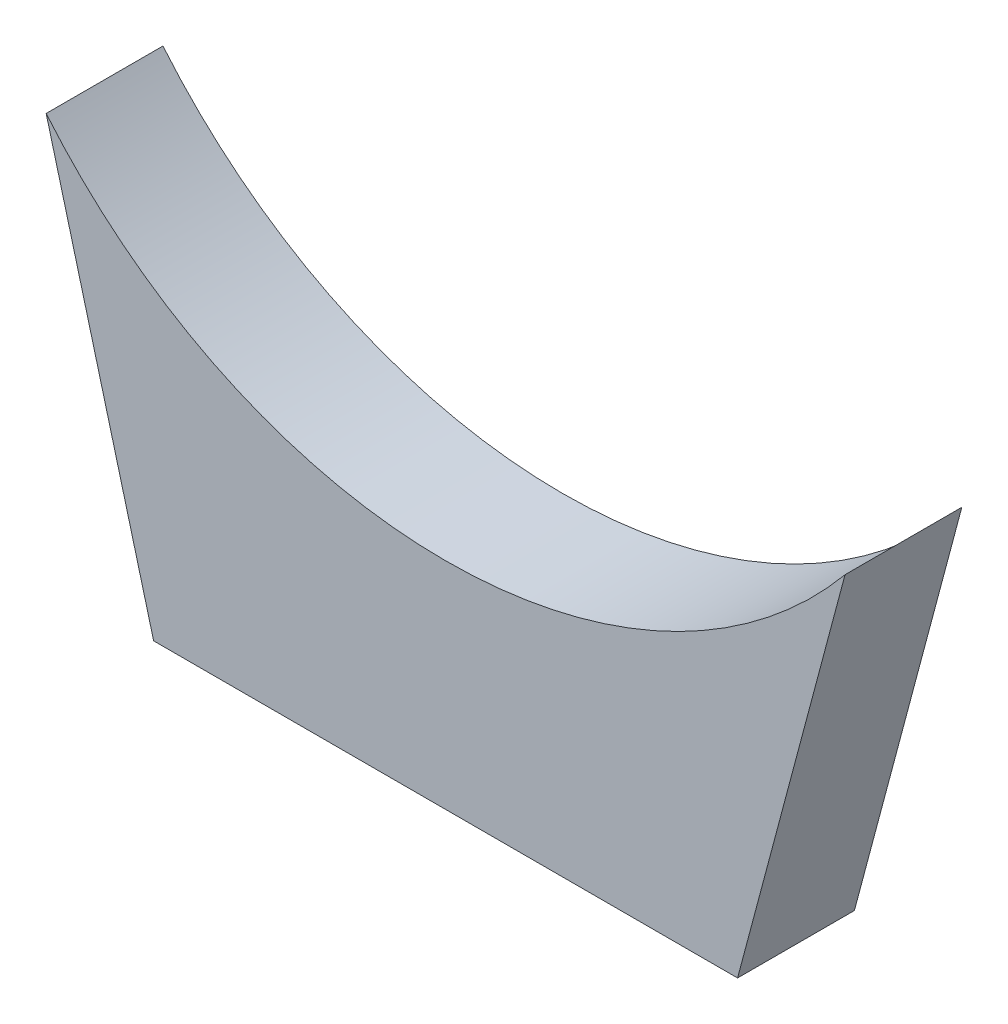
SolidWorks part; units mm, degrees
ref_plane "Front Plane" through (0, 0, 0) normal (0, 0, 1) x (1, 0, 0)
ref_plane "Top Plane" through (0, 0, 0) normal (0, 1, 0) x (1, 0, 0)
ref_plane "Right Plane" through (0, 0, 0) normal (1, 0, 0) x (0, 0, -1)
sketch3d "3DSketch2"
  line L0 (5.5285, 112.0637, 175.5826) -> (-96.0715, 493.0637, 175.5826) construction
  line L1 (-96.0715, 493.0637, 175.5826) -> (5.5285, 112.0637, 175.5826) construction
  line L2 (5.5285, 112.0637, 175.5826) -> (-27.1946, 234.7755, 175.5826) construction
  line L3 (183.3285, 112.0637, 175.5826) -> (284.9285, 493.0637, 175.5826) construction
  line L4 (183.3285, 112.0637, 175.5826) -> (216.0517, 234.7755, 175.5826) construction
  line L5 (-27.1946, 234.7755, 175.5826) -> (216.0517, 234.7755, 175.5826) construction
  line L6 (94.4285, 234.7755, 175.5826) -> (94.4285, 177.6255, 175.5826) construction
  line L7 (-27.1946, 234.7755, 175.5826) -> (5.5285, 112.0637, 175.5826)
  line L8 (5.5285, 112.0637, 175.5826) -> (183.3285, 112.0637, 175.5826)
  line L9 (183.3285, 112.0637, 175.5826) -> (216.0517, 234.7755, 175.5826)
  circle A0 centre (183.3285, 112.0637, 175.5826) radius 17.78 construction
  circle A1 centre (284.9285, 493.0637, 175.5826) radius 17.78 construction
  arc A2 (-27.1946, 234.7755, 175.5826) -> (216.0517, 234.7755, 175.5826) centre (94.4285, 335.616, 175.5826) cw
  point P9 (178.7473, 94.884, 175.5826)
  point P12 (280.3473, 475.884, 175.5826)
  point P17 (94.4285, 335.616, 333.5731)
  point P20 (94.4285, 112.0637, 175.5826)
  dimension "D4" = 157.9905
  dimension "D5" = 223.5523
  dimension "D1" = 127
  dimension "D2" = 127
  dimension "D3" = 57.15
ref_plane "Plane1" through (5.5285, 112.0637, 175.5826) normal (1, 0, 0) x (0, 0, -1)
extrude "Boss-Extrude1" add sketch "3DSketch2" along direction (0, 0, 1) on the side of the normal blind 35.56 contours L9 A2 L7 L8
